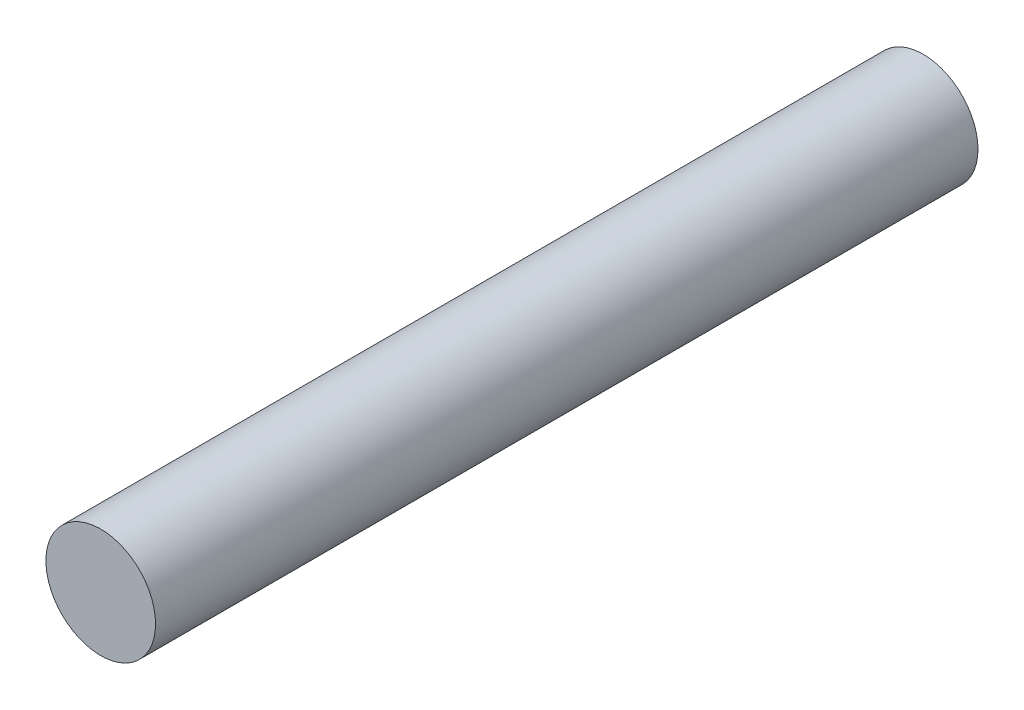
SolidWorks part; units mm, degrees
material "合金钢"
ref_plane "前视基准面" through (0, 0, 0) normal (0, 0, 1) x (1, 0, 0)
ref_plane "上视基准面" through (0, 0, 0) normal (0, 1, 0) x (1, 0, 0)
ref_plane "右视基准面" through (0, 0, 0) normal (1, 0, 0) x (0, 0, -1)
sketch "草图1" plane through (0, 0, 0) normal (0, 0, 1) x (1, 0, 0)
  circle A0 centre (0, 0) radius 2
  dimension "D1" = 4
extrude "凸台-拉伸1" add sketch "草图1" along normal blind 30
